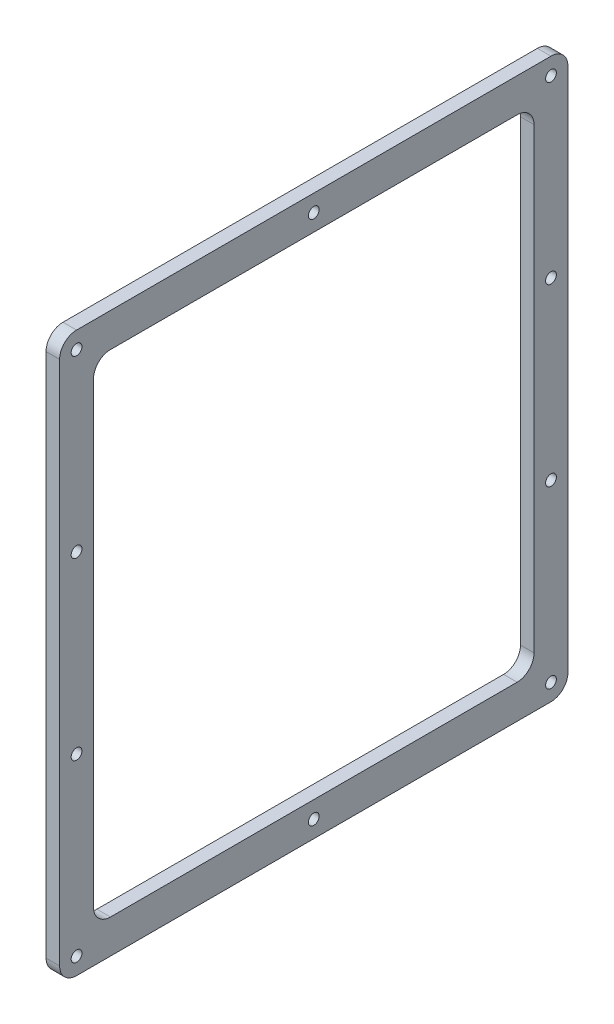
SolidWorks part; units mm, degrees
material "5052-H32"
ref_plane "Front Plane" through (0, 0, 0) normal (0, 0, 1) x (1, 0, 0)
ref_plane "Top Plane" through (0, 0, 0) normal (0, 1, 0) x (1, 0, 0)
ref_plane "Right Plane" through (0, 0, 0) normal (1, 0, 0) x (0, 0, -1)
sketch "Sketch1" plane through (0, 0, 0) normal (1, 0, 0) x (0, 0, -1)
  line L1 (0, 0) -> (190.5, 0)
  line L2 (0, 0) -> (0, 209.55)
  line L3 (0, 209.55) -> (190.5, 209.55)
  line L4 (190.5, 0) -> (190.5, 209.55)
  line L5 (12.7, 196.85) -> (177.8, 196.85)
  line L6 (12.7, 196.85) -> (12.7, 12.7)
  line L7 (12.7, 12.7) -> (177.8, 12.7)
  line L8 (177.8, 196.85) -> (177.8, 12.7)
  dimension "D3" = 12.7
  dimension "D5" = 12.7
  dimension "D1" = 190.5
  dimension "D2" = 209.55
  dimension "D4" = 12.7
  dimension "D6" = 12.7
extrude "Boss-Extrude2" add sketch "Sketch1" along normal blind 5.08
sketch "Sketch2" plane through (5.08, 0, 0) normal (1, 0, 0) x (0, 0, -1)
  line L0 (95.25, 209.55) -> (95.25, 0) construction
  line L1 (190.5, 209.55) -> (0, 209.55) construction
  line L2 (0, 0) -> (190.5, 0) construction
  circle A0 centre (95.25, 115.861) radius 14.2875 construction
  circle A1 centre (95.25, 115.861) radius 14.2875
hole_wizard "#10-32 Tapped Hole1" positions "Sketch7" profile "Sketch8" tap size "#10-32" standard "ANSI Inch" end condition through all
sketch "Sketch7" plane through (5.08, 0, 0) normal (1, 0, 0) x (0, 0, -1)
  line L1 (6.35, 203.2) -> (184.15, 203.2)
  line L2 (6.35, 203.2) -> (6.35, 6.35)
  line L3 (6.35, 6.35) -> (184.15, 6.35)
  line L4 (184.15, 203.2) -> (184.15, 6.35)
  line L5 (6.35, 71.9667) -> (184.15, 71.9667) construction
  line L6 (6.35, 137.5833) -> (184.15, 137.5833) construction
  line L10 (95.25, 203.2) -> (95.25, 137.5833) construction
  line L11 (95.25, 137.5833) -> (95.25, 71.9667) construction
  line L12 (95.25, 71.9667) -> (95.25, 6.35) construction
  line L14 (190.5, 209.55) -> (0, 209.55) construction
  line L15 (0, 0) -> (190.5, 0) construction
  line L16 (0, 209.55) -> (0, 0) construction
  line L17 (190.5, 0) -> (190.5, 209.55) construction
  point P1 (6.35, 203.2)
  point P2 (184.15, 6.35)
  point P157 (6.35, 6.35)
  point P158 (184.15, 203.2)
  point P168 (95.25, 6.35)
  point P170 (95.25, 203.2)
  point P172 (6.35, 137.5833)
  point P174 (6.35, 71.9667)
  point P176 (184.15, 71.9667)
  point P179 (184.15, 137.5833)
  dimension "D1" = 6.35
  dimension "D2" = 6.35
  dimension "D3" = 6.35
  dimension "D4" = 6.35
sketch "Sketch8" plane through (5.08, 203.2, -6.35) normal (0, 1, 0) x (0, 0, -1)
  line L0 (0, 0) -> (0, 5.08)
  line L1 (0, 5.08) -> (2.0193, 5.08)
  line L2 (2.0193, 5.08) -> (2.0193, 0)
  line L5 (2.0193, 0) -> (0, 0)
  line L11 (0, -6.35) -> (0, 107.95) construction
  dimension "Thru Tap Drill Dia." = 4.0386
  dimension "Thru Tap Drill Depth" = 5.08
cosmetic thread "Hole Thread1" parameters "D2"=4.826
cosmetic thread "Hole Thread2" parameters "D2"=4.826
cosmetic thread "Hole Thread3" parameters "D2"=4.826
cosmetic thread "Hole Thread4" parameters "D2"=4.826
cosmetic thread "Hole Thread5" parameters "D2"=4.826
cosmetic thread "Hole Thread6" parameters "D2"=4.826
cosmetic thread "Hole Thread7" parameters "D2"=4.826
cosmetic thread "Hole Thread8" parameters "D2"=4.826
cosmetic thread "Hole Thread9" parameters "D2"=4.826
cosmetic thread "Hole Thread10" parameters "D2"=4.826
fillet "Fillet1" radius 6.35 8 edges at (2.54, 12.7, -177.8) (2.54, 0, -190.5) (2.54, 209.55, -190.5) (2.54, 196.85, -177.8) (2.54, 209.55, 0) (2.54, 196.85, -12.7) (2.54, 0, 0) (2.54, 12.7, -12.7)
